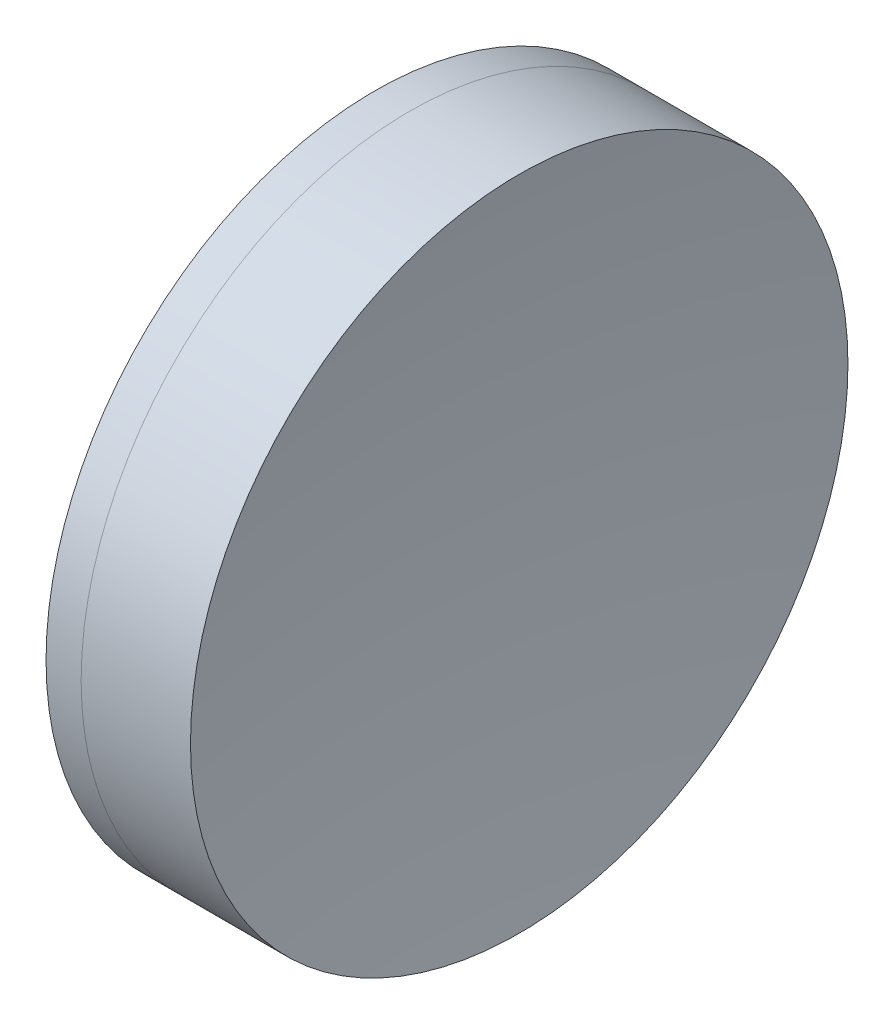
SolidWorks part; units mm, degrees
ref_plane "前视基准面" through (0, 0, 0) normal (0, 0, 1) x (1, 0, 0)
ref_plane "上视基准面" through (0, 0, 0) normal (0, 1, 0) x (1, 0, 0)
ref_plane "右视基准面" through (0, 0, 0) normal (1, 0, 0) x (0, 0, -1)
sketch "草图1" plane through (0, 0, 0) normal (0, 1, 0) x (1, 0, 0)
  line L0 (124.5233, 0) -> (646.9917, 0) construction
  line L1 (352.5016, -12.7) -> (353.8572, -12.7)
  line L2 (352.5016, 12.7) -> (353.8572, 12.7)
  arc A0 (353.8572, -12.7) -> (353.8572, 12.7) centre (292.4059, 0) ccw
  arc A1 (352.5016, 12.7) -> (352.5016, -12.7) centre (411.7559, 0) ccw
  point P10 (351.1559, 0)
  point P11 (355.1559, 0)
  dimension "D3" = 60.6
  dimension "D4" = 62.75
  dimension "D1" = 12.7
  dimension "D2" = 12.7
  dimension "D5" = 4
revolve "旋转1" add sketch "草图1" angle 360 about L0
sketch "草图2" plane through (0, 0, 0) normal (0, 1, 0) x (1, 0, 0)
  line L0 (-0.5519, 0) -> (622.6607, 0) construction
  line L2 (353.8572, 12.7) -> (358.0817, 12.7)
  line L3 (353.8572, -12.7) -> (358.0817, -12.7)
  arc A0 (358.0817, 12.7) -> (358.0817, -12.7) centre (444.7259, 0) ccw
  arc A1 (353.8572, -12.7) -> (353.8572, 12.7) centre (292.4059, 0) ccw construction
  arc A2 (353.8572, -12.7) -> (353.8572, 12.7) centre (292.4059, 0) ccw
  point P4 (355.1559, 0)
  point P8 (357.1559, 0)
  dimension "D1" = 87.57
  dimension "D2" = 2
revolve "旋转3" add sketch "草图2" angle 360 about L0
